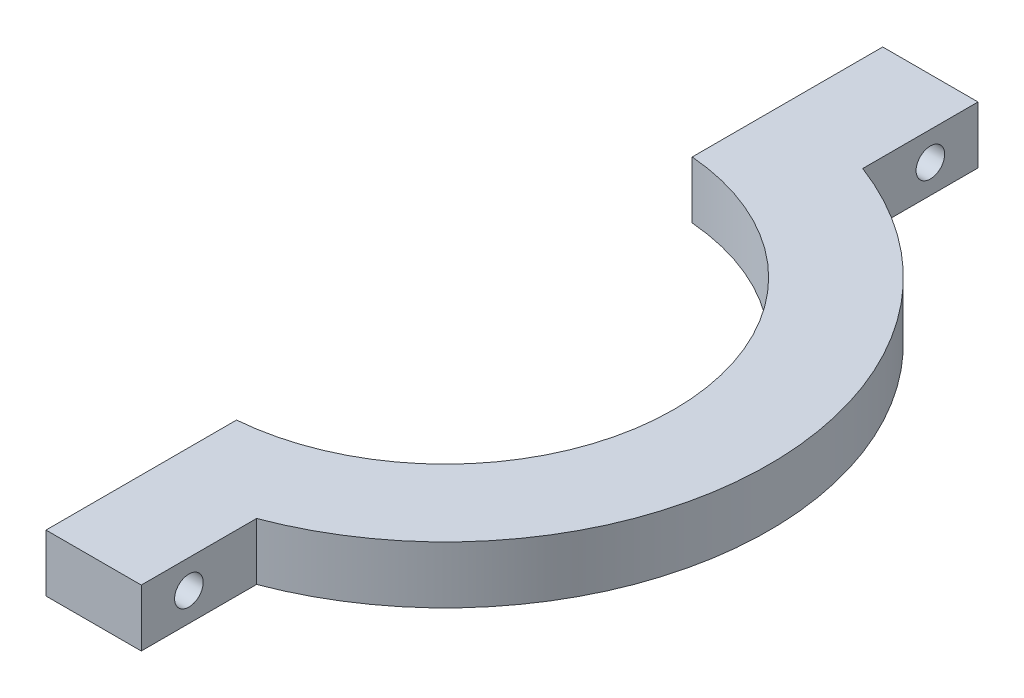
SolidWorks part; units mm, degrees
ref_plane "Front Plane" through (0, 0, 0) normal (0, 0, 1) x (1, 0, 0)
ref_plane "Top Plane" through (0, 0, 0) normal (0, 1, 0) x (1, 0, 0)
ref_plane "Right Plane" through (0, 0, 0) normal (1, 0, 0) x (0, 0, -1)
sketch "Sketch1" plane through (0, 0, 0) normal (0, 1, 0) x (1, 0, 0)
  line L0 (2, 43.9165) -> (2, 23.9165)
  line L1 (2, -23.9165) -> (2, -43.9165)
  line L2 (2, 43.9165) -> (12, 43.9165)
  line L3 (12, 43.9165) -> (12, 31.8119)
  line L4 (2, -43.9165) -> (12, -43.9165)
  line L5 (12, -43.9165) -> (12, -31.8119)
  arc A0 (2, -23.9165) -> (2, 23.9165) centre (0, 0) ccw
  arc A1 (12, -31.8119) -> (33.8674, 3) centre (0, 0) ccw
  arc A2 (33.8674, 3) -> (12, 31.8119) centre (0, 0) ccw
  point P13 (0, 0)
  dimension "D1" = 48
  dimension "D4" = 10
  dimension "D2" = 2
  dimension "D3" = 10
  dimension "D5" = 20
  dimension "D6" = 20
  dimension "D7" = 10
extrude "Boss-Extrude1" add sketch "Sketch1" along normal blind 6
sketch "Sketch4" plane through (12, 0, 0) normal (1, 0, 0) x (0, 0, -1)
  line L0 (-43.9165, 6) -> (-31.8119, 6) construction
  line L1 (-43.9165, 6) -> (-43.9165, 0) construction
  circle A0 centre (-38.9165, 3) radius 1.5
  dimension "D1" = 3
  dimension "D2" = 3
  dimension "D3" = 5
extrude "Cut-Extrude3" cut sketch "Sketch4" against normal through all
mirror "Mirror1" about plane through (0, 0, 0) normal (0, 0, 1) of "Cut-Extrude3"
